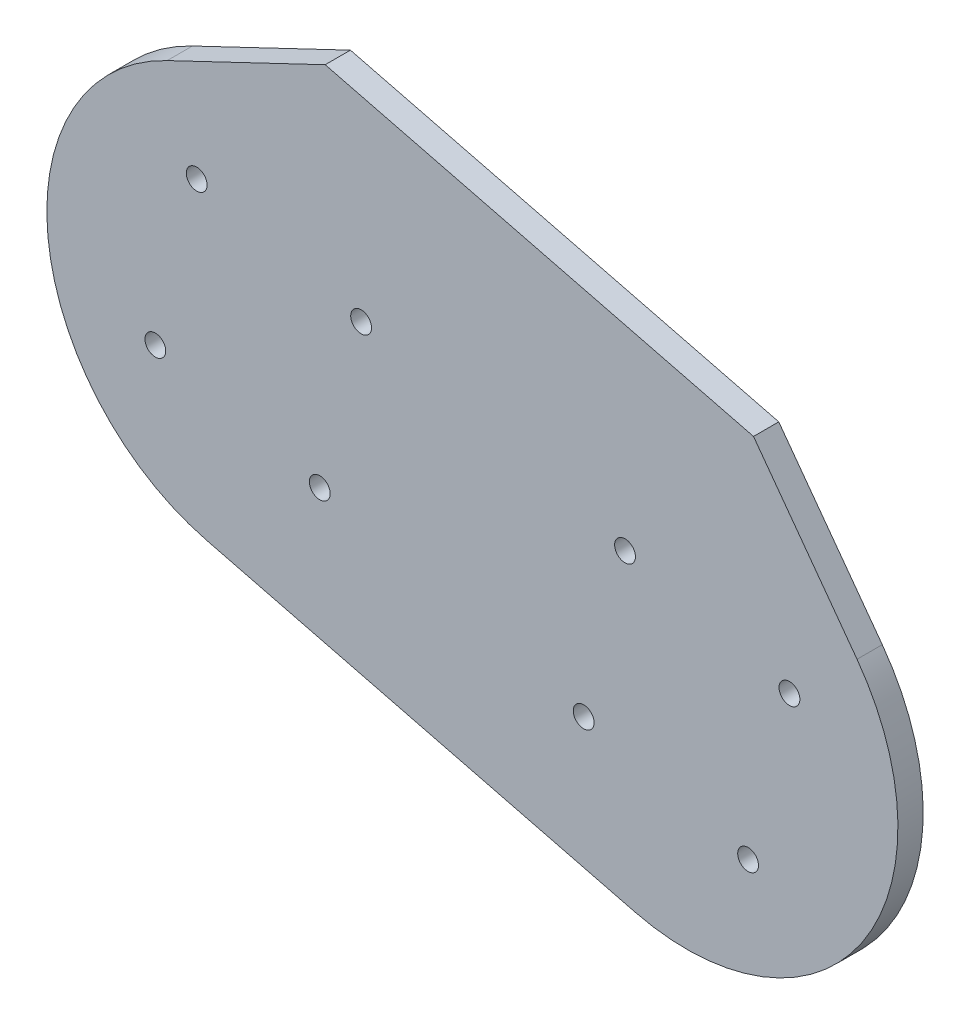
SolidWorks part; units mm, degrees
ref_plane "前视基准面" through (0, 0, 0) normal (0, 0, 1) x (1, 0, 0)
ref_plane "上视基准面" through (0, 0, 0) normal (0, 1, 0) x (1, 0, 0)
ref_plane "右视基准面" through (0, 0, 0) normal (1, 0, 0) x (0, 0, -1)
sketch "草图1" plane through (0, 0, 0) normal (0, 0, 1) x (1, 0, 0)
  line L1 (356.9788, -329.3887) -> (424.864, -346.4653)
  line L2 (375.7631, -254.7151) -> (443.6482, -271.7916)
  line L3 (375.7631, -254.7151) -> (350.7207, -266.6682)
  line L4 (443.6482, -271.7916) -> (460.0542, -294.1712)
  circle A0 centre (355.3996, -280.5942) radius 1.65
  circle A1 centre (381.4578, -287.1492) radius 1.65
  circle A2 centre (348.8446, -306.6525) radius 1.65
  circle A3 centre (374.9028, -313.2074) radius 1.65
  circle A4 centre (423.2847, -297.6708) radius 1.65
  circle A5 centre (449.3429, -304.2258) radius 1.65
  circle A6 centre (416.7297, -323.729) radius 1.65
  circle A7 centre (442.788, -330.284) radius 1.65
  circle A8 centre (365.1512, -296.9008) radius 28.5 construction
  arc A10 (350.7207, -266.6682) -> (356.9788, -329.3887) centre (365.1512, -296.9008) ccw
  arc A11 (424.864, -346.4653) -> (460.0542, -294.1712) centre (433.0363, -313.9774) ccw
  circle A14 centre (365.1512, -296.9008) radius 33.5 construction
  dimension "D1" = 5
extrude "凸台-拉伸1" add sketch "草图1" along normal blind 4
